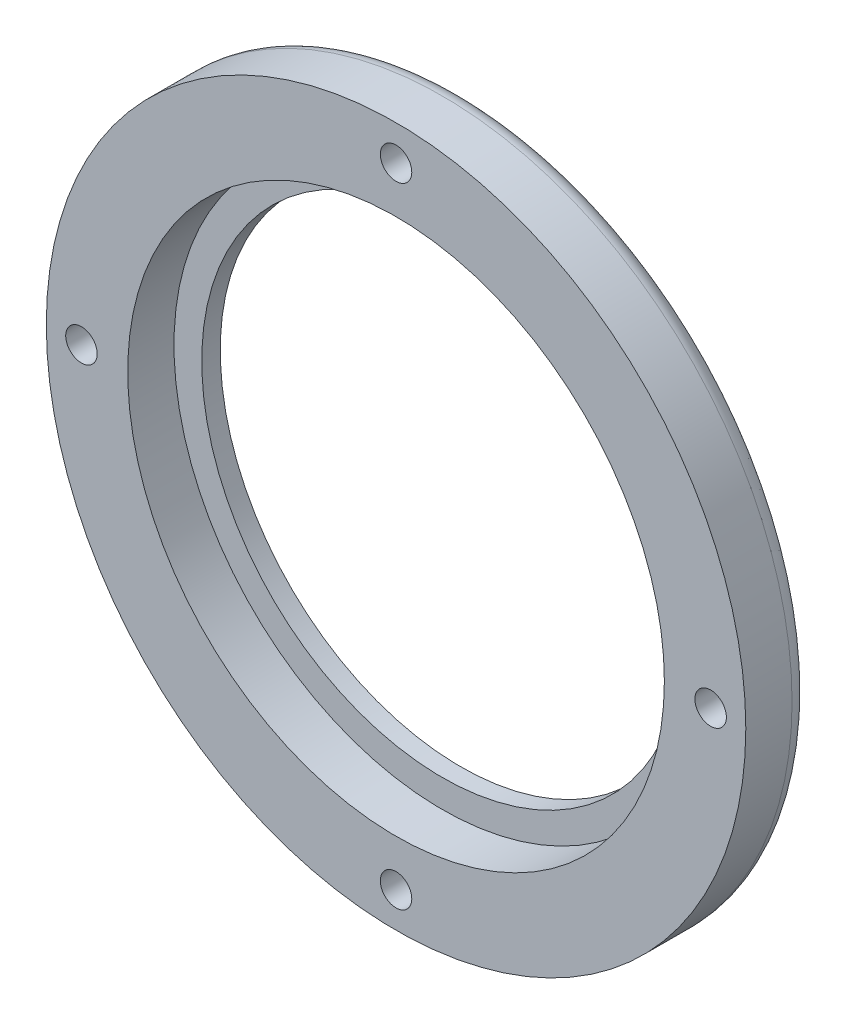
SolidWorks part; units mm, degrees
ref_plane "前视基准面" through (0, 0, 0) normal (0, 0, 1) x (1, 0, 0)
ref_plane "上视基准面" through (0, 0, 0) normal (0, 1, 0) x (1, 0, 0)
ref_plane "右视基准面" through (0, 0, 0) normal (1, 0, 0) x (0, 0, -1)
other "Configuration Table"
sketch "草图1" plane through (0, 0, 0) normal (0, 0, 1) x (1, 0, 0)
  circle A0 centre (0, 0) radius 26
  circle A1 centre (0, 0) radius 37.8
extrude "凸台-拉伸1" add sketch "草图1" along normal blind 7
sketch "草图2" plane through (0, 0, 7) normal (0, 0, 1) x (1, 0, 0)
  circle A0 centre (0, 0) radius 29
extrude "切除-拉伸1" cut sketch "草图2" against normal blind 5
fillet "圆角1" radius 2 1 edges at (37.8, 0, 0)
sketch "草图3" plane through (0, 0, 7) normal (0, 0, 1) x (1, 0, 0)
  line L0 (0, 0) -> (0, -34) construction
  circle A0 centre (0, -34) radius 1.7
  circle A1 centre (-34, 0) radius 1.7
  circle A2 centre (0, 34) radius 1.7
  circle A3 centre (34, 0) radius 1.7
  point P13 (0, 0)
  dimension "D1" = 4
extrude "切除-拉伸2" cut sketch "草图3" against normal blind 8
sketch "草图4" plane through (0, 0, 0) normal (0, 0, -1) x (-1, 0, 0)
  circle A1 centre (-34, 0) radius 2.9
  circle A2 centre (0, 34) radius 2.9
  circle A3 centre (34, 0) radius 2.9
  circle A4 centre (0, -34) radius 2.9
  point P13 (0, 0)
  dimension "D1" = 4
extrude "切除-拉伸3" cut sketch "草图4" against normal blind 2.5
